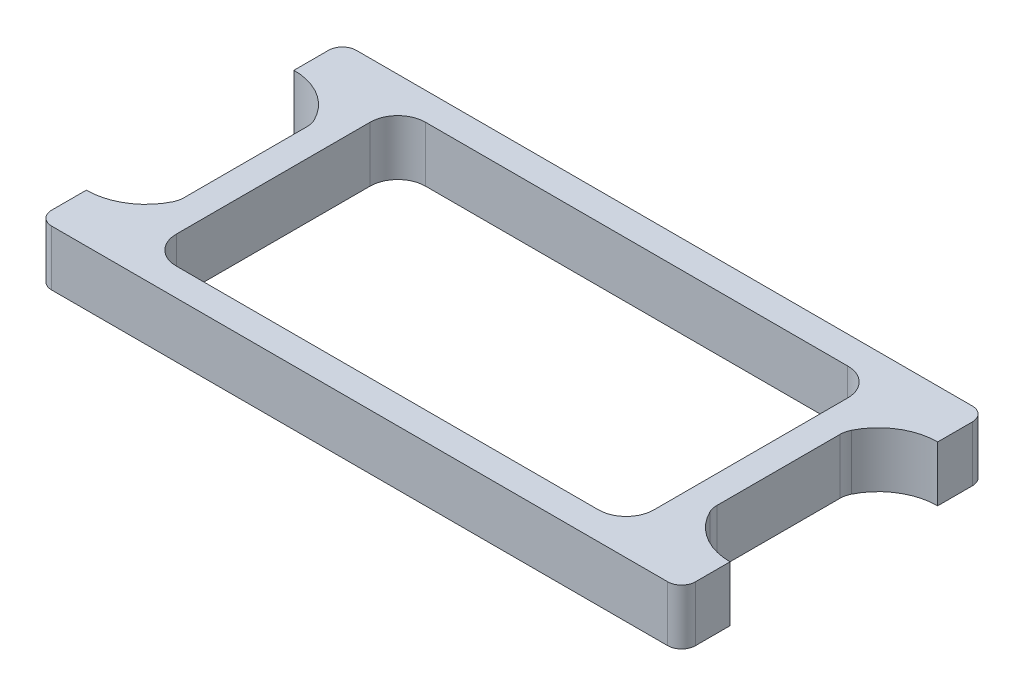
SolidWorks part; units mm, degrees
ref_plane "Front Plane" through (0, 0, 0) normal (0, 0, 1) x (1, 0, 0)
ref_plane "Top Plane" through (0, 0, 0) normal (0, 1, 0) x (1, 0, 0)
ref_plane "Right Plane" through (0, 0, 0) normal (1, 0, 0) x (0, 0, -1)
sketch "Sketch1" plane through (0, 0, 0) normal (0, 1, 0) x (1, 0, 0)
  line L1 (46.5, -22) -> (-46.5, -22)
  line L2 (46.5, -22) -> (46.5, 22)
  line L3 (46.5, 22) -> (-46.5, 22)
  line L4 (-46.5, -22) -> (-46.5, 22)
  line L5 (46.5, -22) -> (-46.5, 22) construction
  line L6 (46.5, 22) -> (-46.5, -22) construction
  point P0 (0, 0)
  dimension "D1" = 44
  dimension "D2" = 93
extrude "Boss-Extrude1" add sketch "Sketch1" along normal blind 8
sketch "Sketch2" plane through (0, 8, 0) normal (0, 1, 0) x (1, 0, 0)
  line L2 (46.5, -22) -> (46.5, 22) construction
  line L3 (-46.5, 22) -> (-46.5, -22) construction
  line L4 (46.5, 22) -> (-46.5, 22) construction
  line L5 (-46.5, -22) -> (46.5, -22) construction
  line L12 (34.5, -18) -> (34.5, 18)
  line L13 (-34.5, -18) -> (34.5, -18)
  line L14 (-34.5, 18) -> (-34.5, -18)
  line L15 (34.5, 18) -> (-34.5, 18)
  dimension "D2" = 12
  dimension "D1" = 12
  dimension "D3" = 4
  dimension "D4" = 4
extrude "Cut-Extrude1" cut sketch "Sketch2" against normal blind 8
fillet "Fillet1" radius 4 4 edges at (34.5, 4, -18) (34.5, 4, 18) (-34.5, 4, 18) (-34.5, 4, -18)
fillet "Fillet2" radius 2 4 edges at (-46.5, 4, -22) (46.5, 4, -22) (-46.5, 4, 22) (46.5, 4, 22)
sketch "Sketch3" plane through (0, 8, 0) normal (0, 1, 0) x (1, 0, 0)
  line L0 (-46.5, 20) -> (-46.5, -20) construction
  line L1 (-53.1735, 0) -> (2.8228, 0) construction
  line L2 (-38.5, 9.5224) -> (-38.5, -9.5224)
  line L3 (-46.5, -15) -> (-46.5, 15)
  arc A0 (-46.5, 15) -> (-38.5, 9.5224) centre (-46.5, 6.4192) cw
  arc A1 (-46.5, -15) -> (-38.5, -9.5224) centre (-46.5, -6.4192) ccw
  point P12 (-38.5, 0)
  dimension "D1" = 8
  dimension "D2" = 30
extrude "Cut-Extrude2" cut sketch "Sketch3" against normal through all both and the other way through all
fillet "Fillet3" radius 3 2 edges at (-38.5, 4, 9.5224) (-38.5, 4, -9.5224)
mirror "Mirror1" about plane through (0, 0, 0) normal (1, 0, 0) of "Cut-Extrude2", "Fillet3"
